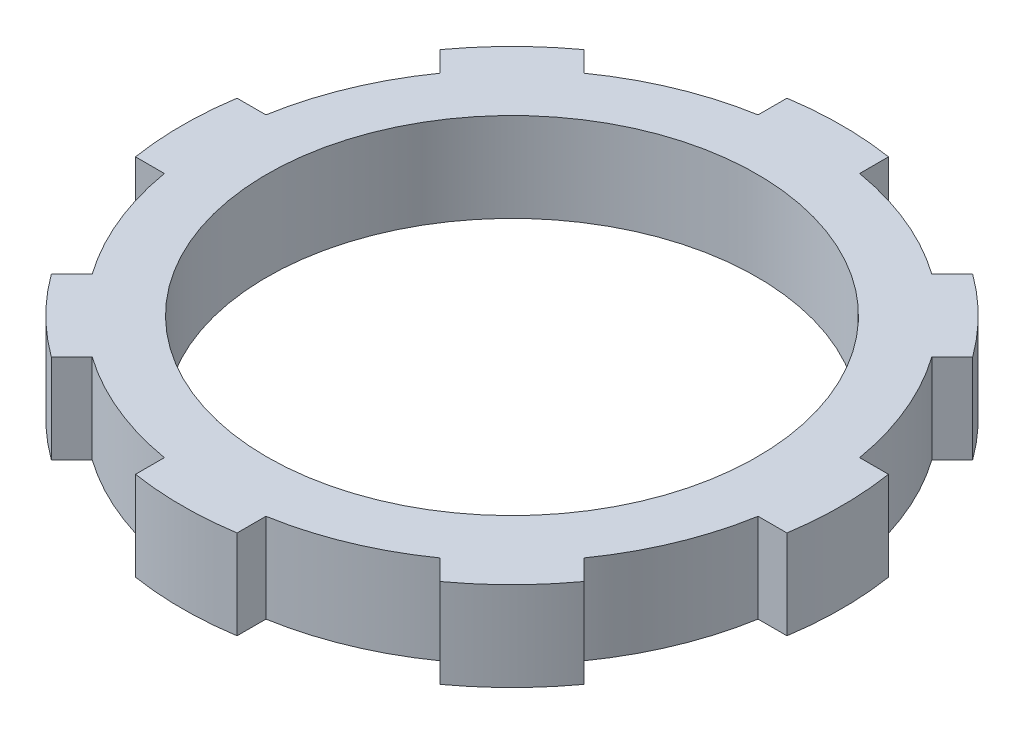
SolidWorks part; units mm, degrees
ref_plane "Спереди" through (0, 0, 0) normal (0, 0, 1) x (1, 0, 0)
ref_plane "Сверху" through (0, 0, 0) normal (0, 1, 0) x (1, 0, 0)
ref_plane "Справа" through (0, 0, 0) normal (1, 0, 0) x (0, 0, -1)
sketch "Эскиз2" plane through (0, 0, 0) normal (0, 1, 0) x (1, 0, 0)
  line L0 (0, 0) -> (0, 31.2721) construction
  line L1 (0, 0) -> (31.178, 0) construction
  line L2 (-2.85, 18.2792) -> (-2.85, 16.658)
  line L3 (2.85, 18.2792) -> (2.85, 16.658)
  line L4 (10.9101, 14.9406) -> (9.7637, 13.7942)
  line L5 (14.9406, 10.9101) -> (13.7942, 9.7637)
  line L6 (18.2792, 2.85) -> (16.658, 2.85)
  line L7 (18.2792, -2.85) -> (16.658, -2.85)
  line L8 (14.9406, -10.9101) -> (13.7942, -9.7637)
  line L9 (10.9101, -14.9406) -> (9.7637, -13.7942)
  line L10 (2.85, -18.2792) -> (2.85, -16.658)
  line L11 (-2.85, -18.2792) -> (-2.85, -16.658)
  line L12 (-10.9101, -14.9406) -> (-9.7637, -13.7942)
  line L13 (-14.9406, -10.9101) -> (-13.7942, -9.7637)
  line L14 (-18.2792, -2.85) -> (-16.658, -2.85)
  line L15 (-18.2792, 2.85) -> (-16.658, 2.85)
  line L16 (-14.9406, 10.9101) -> (-13.7942, 9.7637)
  line L17 (-10.9101, 14.9406) -> (-9.7637, 13.7942)
  arc A0 (-13.7942, 9.7637) -> (-16.658, 2.85) centre (0, 0) ccw
  arc A1 (-10.9101, 14.9406) -> (-14.9406, 10.9101) centre (0, 0) ccw
  circle A2 centre (0, 0) radius 13.75
  arc A3 (-18.2792, 2.85) -> (-18.2792, -2.85) centre (0, 0) ccw
  arc A4 (-16.658, -2.85) -> (-13.7942, -9.7637) centre (0, 0) ccw
  arc A5 (-14.9406, -10.9101) -> (-10.9101, -14.9406) centre (0, 0) ccw
  arc A6 (-9.7637, -13.7942) -> (-2.85, -16.658) centre (0, 0) ccw
  arc A7 (-2.85, -18.2792) -> (2.85, -18.2792) centre (0, 0) ccw
  arc A8 (2.85, -16.658) -> (9.7637, -13.7942) centre (0, 0) ccw
  arc A9 (10.9101, -14.9406) -> (14.9406, -10.9101) centre (0, 0) ccw
  arc A10 (13.7942, -9.7637) -> (16.658, -2.85) centre (0, 0) ccw
  arc A11 (18.2792, -2.85) -> (18.2792, 2.85) centre (0, 0) ccw
  arc A12 (16.658, 2.85) -> (13.7942, 9.7637) centre (0, 0) ccw
  arc A13 (14.9406, 10.9101) -> (10.9101, 14.9406) centre (0, 0) ccw
  arc A14 (9.7637, 13.7942) -> (2.85, 16.658) centre (0, 0) ccw
  arc A15 (2.85, 18.2792) -> (-2.85, 18.2792) centre (0, 0) ccw
  arc A16 (-2.85, 16.658) -> (-9.7637, 13.7942) centre (0, 0) ccw
  point P41 (0, 0)
  dimension "D1" = 37
  dimension "D2" = 33.8
  dimension "D3" = 27.5
  dimension "D4" = 5.7
  dimension "D5" = 8
extrude "Бобышка-Вытянуть1" add sketch "Эскиз2" along normal blind 5
